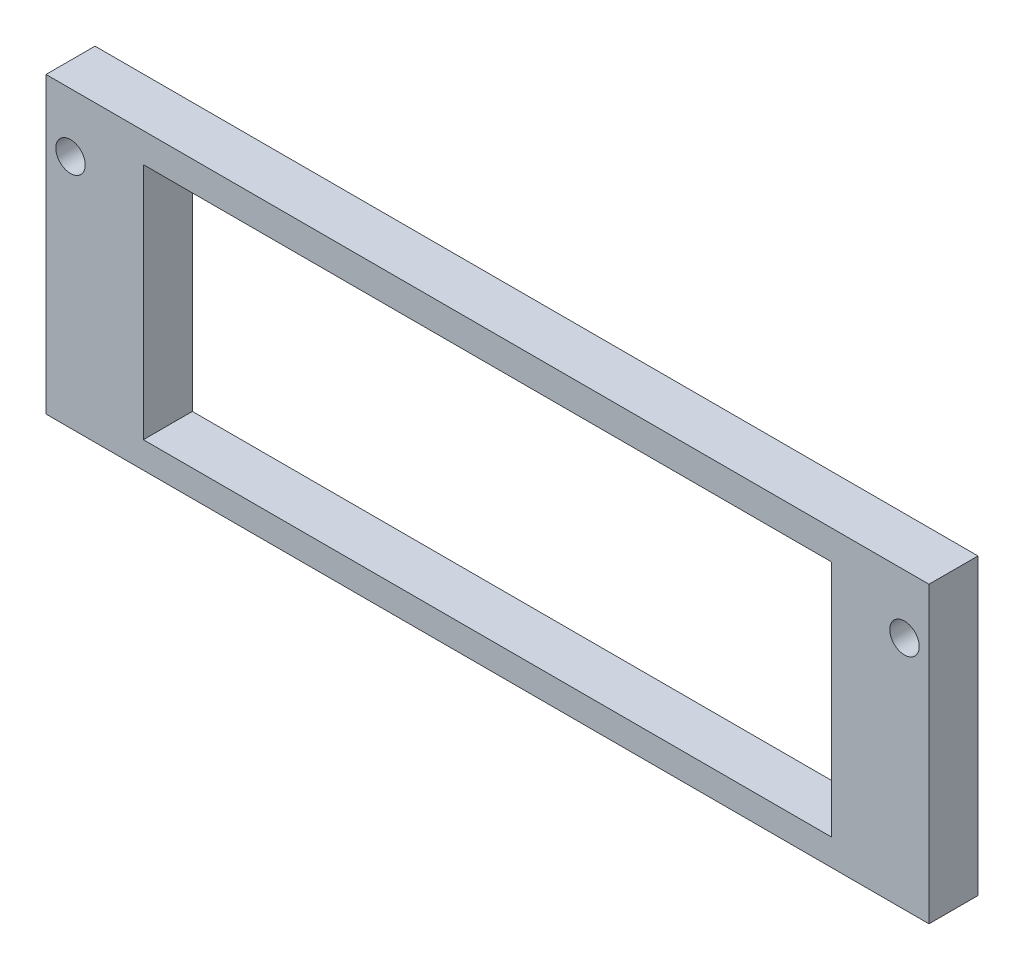
SolidWorks part; units mm, degrees
material "Acrílico (médio-alto impacto)"
ref_plane "Plano frontal" through (0, 0, 0) normal (0, 0, 1) x (1, 0, 0)
ref_plane "Plano superior" through (0, 0, 0) normal (0, 1, 0) x (1, 0, 0)
ref_plane "Plano direito" through (0, 0, 0) normal (1, 0, 0) x (0, 0, -1)
sketch "Esboço1" plane through (0, 0, 0) normal (0, 0, 1) x (1, 0, 0)
  line L1 (-25.221, 16.8623) -> (64.839, 16.8623)
  line L2 (-25.221, 16.8623) -> (-25.221, -13.1377)
  line L3 (-25.221, -13.1377) -> (64.839, -13.1377)
  line L4 (64.839, 16.8623) -> (64.839, -13.1377)
  dimension "D1" = 30
  dimension "D2" = 90.06
extrude "Ressalto-extrusão1" add sketch "Esboço1" along normal blind 5
sketch "Esboço2" plane through (0, 0, 0) normal (0, 0, -1) x (-1, 0, 0)
  line L1 (-54.909, 13.8623) -> (15.291, 13.8623)
  line L2 (-54.909, 13.8623) -> (-54.909, -10.4377)
  line L3 (-54.909, -10.4377) -> (15.291, -10.4377)
  line L4 (15.291, 13.8623) -> (15.291, -10.4377)
  line L6 (-64.839, -13.1377) -> (-64.839, 16.8623) construction
  line L7 (25.221, 16.8623) -> (25.221, -13.1377) construction
  line L9 (25.221, -13.1377) -> (-64.839, -13.1377) construction
  line L10 (-64.839, 16.8623) -> (25.221, 16.8623) construction
  dimension "D1" = 70.2
  dimension "D2" = 24.3
  dimension "D3" = 9.93
  dimension "D4" = 9.93
  dimension "D5" = 2.7
  dimension "D6" = 3
extrude "Corte-extrusão1" cut sketch "Esboço2" against normal through all
sketch "Esboço4" plane through (0, 0, 0) normal (0, 0, -1) x (-1, 0, 0)
  line L1 (-64.839, 16.8623) -> (25.221, 16.8623) construction
  line L2 (-64.839, -13.1377) -> (-64.839, 16.8623) construction
  line L3 (25.221, 16.8623) -> (25.221, -13.1377) construction
  circle A0 centre (22.721, 10.8623) radius 1.5
  circle A2 centre (-62.339, 10.8623) radius 1.5
  dimension "D2" = 3
  dimension "D4" = 6
  dimension "D6" = 2.5
  dimension "D8" = 3
  dimension "D10" = 6
  dimension "D11" = 2.5
extrude "Corte-extrusão2" cut sketch "Esboço4" against normal blind 10
